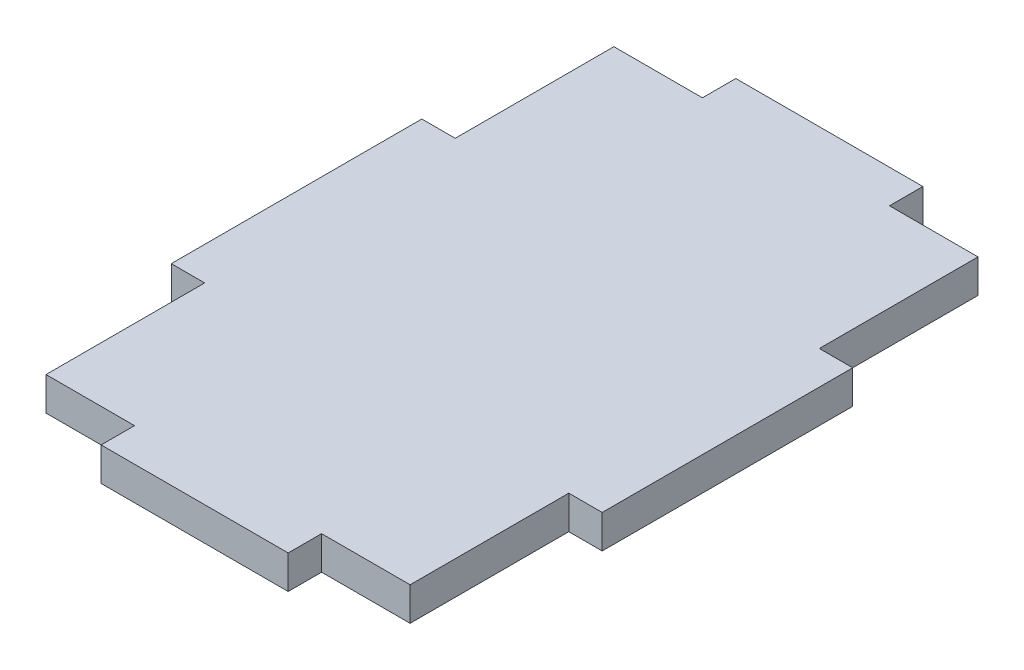
SolidWorks part; units mm, degrees
ref_plane "Front Plane" through (0, 0, 0) normal (0, 0, 1) x (1, 0, 0)
ref_plane "Top Plane" through (0, 0, 0) normal (0, 1, 0) x (1, 0, 0)
ref_plane "Right Plane" through (0, 0, 0) normal (1, 0, 0) x (0, 0, -1)
sketch "Sketch2" plane through (0, 0, 0) normal (0, 1, 0) x (1, 0, 0)
  line L0 (-41.1188, 0) -> (70.5469, 0) construction
  line L5 (0, 74.175) -> (0, -43.8063) construction
  line L6 (-27.25, 18.75) -> (-32.25, 18.75)
  line L7 (-27.25, 42.5) -> (-14, 42.5)
  line L8 (-27.25, 42.5) -> (-27.25, 18.75)
  line L9 (-27.25, -42.5) -> (-14, -42.5)
  line L10 (27.25, 42.5) -> (27.25, 18.75)
  line L11 (-32.25, 18.75) -> (-32.25, -18.75)
  line L12 (-32.25, -18.75) -> (-27.25, -18.75)
  line L13 (-14, 42.5) -> (-14, 47.5)
  line L14 (-14, 47.5) -> (14, 47.5)
  line L15 (14, 47.5) -> (14, 42.5)
  line L16 (32.25, -18.75) -> (27.25, -18.75)
  line L19 (32.25, 18.75) -> (32.25, -18.75)
  line L20 (27.25, 18.75) -> (32.25, 18.75)
  line L21 (14, -47.5) -> (14, -42.5)
  line L22 (-14, -47.5) -> (14, -47.5)
  line L23 (-14, -42.5) -> (-14, -47.5)
  line L24 (-27.25, -18.75) -> (-27.25, -42.5)
  line L25 (-27.25, 18.75) -> (-27.25, 0) construction
  line L26 (-27.25, 0) -> (-27.25, -18.75) construction
  line L27 (14, -42.5) -> (27.25, -42.5)
  line L28 (-14, -42.5) -> (14, -42.5) construction
  line L29 (27.25, -18.75) -> (27.25, -42.5)
  line L30 (27.25, 0) -> (27.25, -18.75) construction
  line L31 (27.25, 18.75) -> (27.25, 0) construction
  line L32 (14, 42.5) -> (27.25, 42.5)
  line L33 (0, 42.5) -> (14, 42.5) construction
  line L34 (-14, 42.5) -> (0, 42.5) construction
  dimension "D1" = 28
  dimension "D2" = 37.5
  dimension "D3" = 54.5
  dimension "D4" = 85
  dimension "D5" = 5
  dimension "D6" = 5
  dimension "D7" = 64.5
extrude "Boss-Extrude1" add sketch "Sketch2" along normal blind 5
